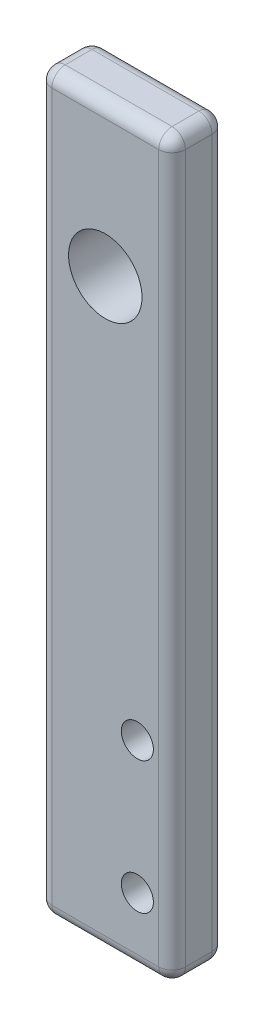
SolidWorks part; units mm, degrees
ref_plane "Front Plane" through (0, 0, 0) normal (0, 0, 1) x (1, 0, 0)
ref_plane "Top Plane" through (0, 0, 0) normal (0, 1, 0) x (1, 0, 0)
ref_plane "Right Plane" through (0, 0, 0) normal (1, 0, 0) x (0, 0, -1)
sketch "Sketch1" plane through (0, 0, 0) normal (0, 0, 1) x (1, 0, 0)
  line L1 (0, 0) -> (10, 0)
  line L2 (0, 0) -> (0, 55)
  line L3 (0, 55) -> (10, 55)
  line L4 (10, 0) -> (10, 55)
  circle A0 centre (7.4, 5) radius 1.2
  circle A1 centre (7.4, 14.9) radius 1.2
  circle A2 centre (5, 43.7929) radius 2.75
extrude "Boss-Extrude1" add sketch "Sketch1" along normal blind 4
fillet "Fillet1" radius 1 12 edges at (5, 0, 4) (5, 0, 0) (0, 0, 2) (10, 0, 2) (10, 55, 2) (0, 55, 2) (0, 27.5, 0) (0, 27.5, 4) (5, 55, 0) (10, 27.5, 0) (10, 27.5, 4) (5, 55, 4)
